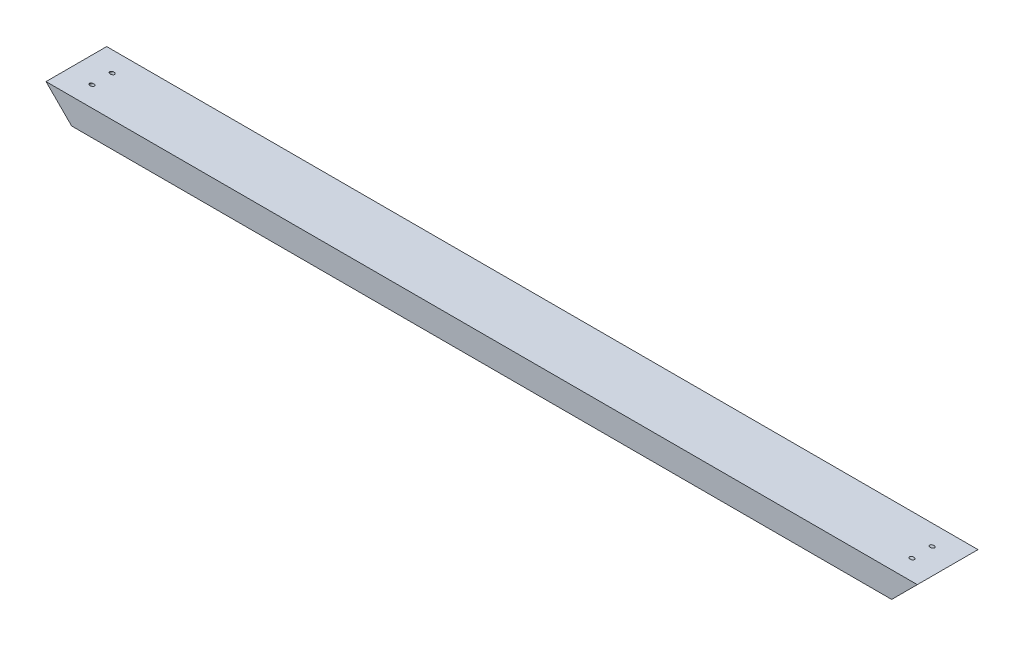
SolidWorks part; units mm, degrees
ref_plane "Front Plane" through (0, 0, 0) normal (0, 0, 1) x (1, 0, 0)
ref_plane "Top Plane" through (0, 0, 0) normal (0, 1, 0) x (1, 0, 0)
ref_plane "Right Plane" through (0, 0, 0) normal (1, 0, 0) x (0, 0, -1)
sketch "Sketch1" plane through (0, 0, 0) normal (0, 0, 1) x (1, 0, 0)
  line L0 (-29.2563, 26.4872) -> (1247.4245, 26.4872)
  line L5 (1247.4245, 26.4872) -> (1209.8319, -11.1054)
  line L8 (-29.2563, 26.4872) -> (8.3363, -11.1054)
  line L9 (8.3363, -11.1054) -> (1209.8319, -11.1054)
  line L10 (1228.6282, 7.6909) -> (-10.46, 7.6909) construction
  point P4 (-10.46, 7.6909)
  point P5 (1228.6282, 7.6909)
  dimension "D1" = 45
  dimension "D2" = 45
  dimension "D3" = 1239.0882
  dimension "D5" = 37.5926
extrude "Boss-Extrude1" add sketch "Sketch1" along normal blind 88.9
sketch "Sketch2" plane through (-1.3846, -1.3846, 0) normal (-0.7071, -0.7071, 0) x (0, 0, 1)
  line L0 (0, 39.4166) -> (0, -13.7473) construction
  circle A0 centre (29.6333, 12.8346) radius 2.5797
  circle A1 centre (59.2667, 12.8346) radius 2.5797
  point P0 (29.6333, 12.8346)
  point P1 (0, 12.8346)
  point P4 (0, 0)
  point P5 (0, 0)
  dimension "D3" = 5.1594
  dimension "D4" = 5.1594
  dimension "D1" = 29.6333
extrude "Cut-Extrude1" cut sketch "Sketch2" against normal through all
sketch "Sketch3" plane through (610.4687, -610.4687, 0) normal (0.7071, -0.7071, 0) x (0, 0, -1)
  line L1 (-88.9, 847.6276) -> (-88.9, 900.7916) construction
  line L2 (0, 847.6276) -> (0, 900.7916) construction
  circle A0 centre (-59.2667, 874.2096) radius 2.5797
  circle A1 centre (-29.6333, 874.2096) radius 2.5797
  point P4 (-88.9, 874.2096)
  point P5 (0, 0)
  point P10 (0, 0)
  point P11 (0, 0)
  dimension "D5" = 5.1594
  dimension "D6" = 5.1594
  dimension "D3" = 29.6333
  dimension "D4" = 29.6333
extrude "Cut-Extrude2" cut sketch "Sketch3" against normal through all
